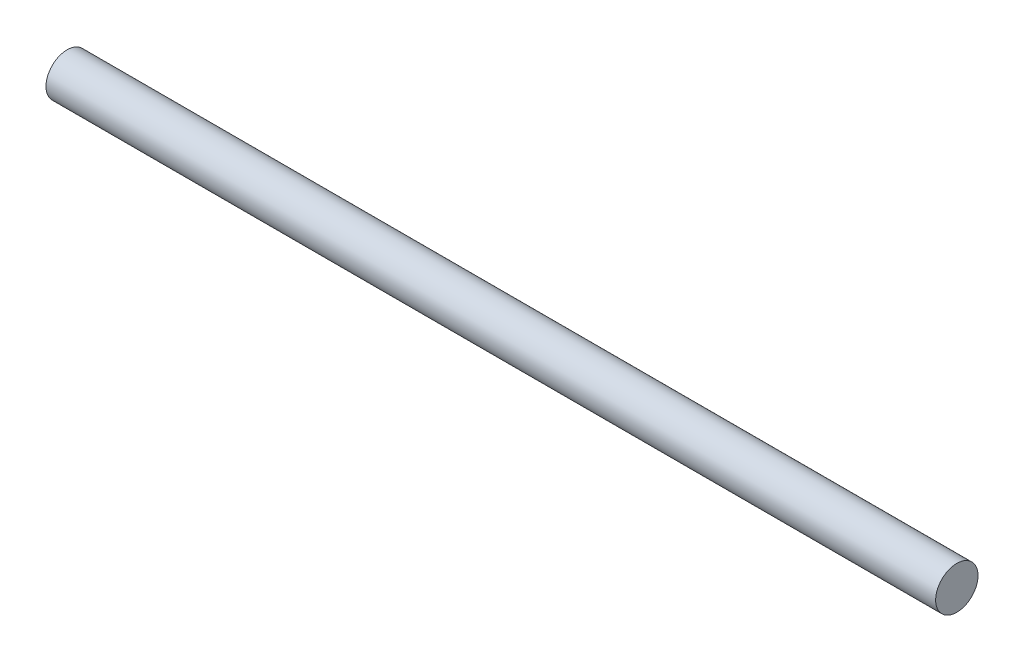
SolidWorks part; units mm, degrees
ref_plane "Alzado" through (0, 0, 0) normal (0, 0, 1) x (1, 0, 0)
ref_plane "Planta" through (0, 0, 0) normal (0, 1, 0) x (1, 0, 0)
ref_plane "Vista lateral" through (0, 0, 0) normal (1, 0, 0) x (0, 0, -1)
sketch "Croquis1" plane through (0, 0, 0) normal (1, 0, 0) x (0, 0, -1)
  circle A0 centre (0, 0) radius 9.525
  dimension "D1" = 19.05
extrude "Saliente-Extruir1" add sketch "Croquis1" along normal blind 400
sketch "Croquis2" plane through (0, 0, 0) normal (-1, 0, 0) x (0, 0, 1)
  circle A0 centre (0, 0) radius 4.7625
  dimension "D1" = 9.525
extrude "Cortar-Extruir1" cut sketch "Croquis2" against normal blind 30
sketch "Croquis3" plane through (400, 0, 0) normal (1, 0, 0) x (0, 0, -1)
  circle A0 centre (0, 0) radius 8.7313
  circle A1 centre (0, 0) radius 9.525
  circle A2 centre (0, 0) radius 9.525 construction
  dimension "D1" = 0.7937
